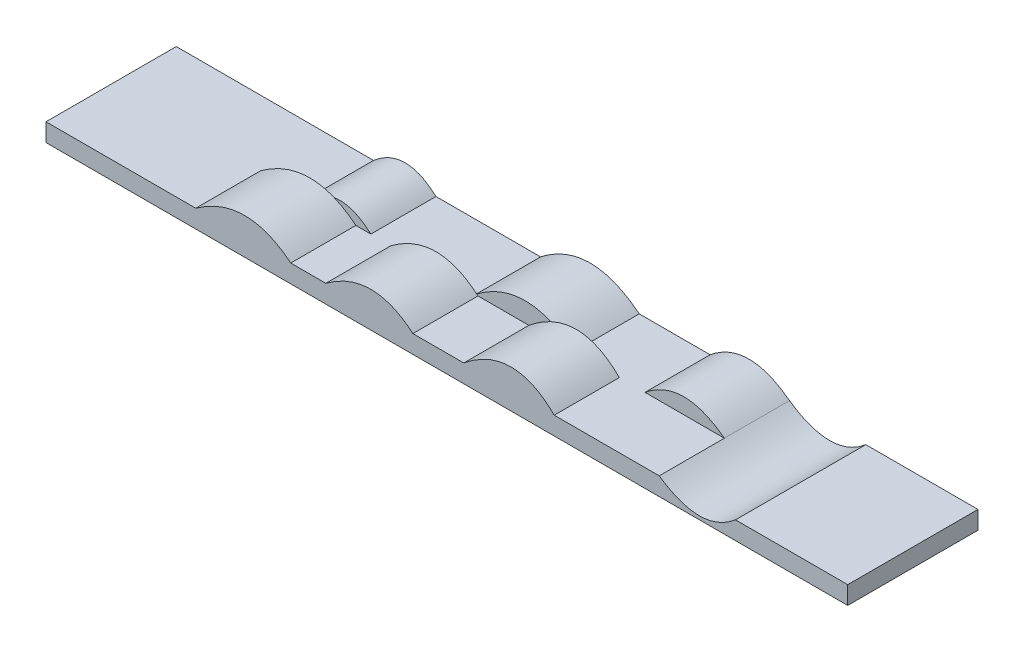
SolidWorks part; units mm, degrees
material "Pine"
ref_plane "Front Plane" through (0, 0, 0) normal (0, 0, 1) x (1, 0, 0)
ref_plane "Top Plane" through (0, 0, 0) normal (0, 1, 0) x (1, 0, 0)
ref_plane "Right Plane" through (0, 0, 0) normal (1, 0, 0) x (0, 0, -1)
sketch "Sketch1" plane through (0, 0, 0) normal (0, 1, 0) x (1, 0, 0)
  line L1 (-2000, -325) -> (2000, -325)
  line L2 (-2000, -325) -> (-2000, 325)
  line L3 (-2000, 325) -> (2000, 325)
  line L4 (2000, -325) -> (2000, 325)
  line L5 (-2000, -325) -> (2000, 325) construction
  line L6 (-2000, 325) -> (2000, -325) construction
  point P0 (0, 0)
  dimension "D1" = 650
  dimension "D2" = 4000
extrude "Boss-Extrude1" add sketch "Sketch1" along normal blind 90
sketch "Sketch2" plane through (0, 0, 325) normal (0, 0, 1) x (1, 0, 0)
  line L0 (-2000, 90) -> (2000, 90) construction
  line L1 (-1252.9038, 90) -> (535.6897, 90)
  spline S0 degree 2 poles (-1252.9038, 90) (-1001.8033, 271.3905) (-778.9548, 90) knots 0 0 0 1 1 1
  spline S1 degree 2 poles (-604.045, 90) (-371.4824, 262.9864) (-169.5917, 90) knots 0 0 0 1 1 1
  spline S2 degree 2 poles (84.3096, 90) (330.4132, 291.4597) (535.6897, 90) knots 0 0 0 1 1 1
  line M3 (2000, 90) -> (-2000, 90)
extrude "Boss-Extrude2" add sketch "Sketch2" against normal blind 325 contours S0 L1 | S1 L1 | S2 M3
sketch "Sketch3" plane through (0, 0, -325) normal (0, 0, -1) x (-1, 0, 0)
  line L0 (-2000, 90) -> (2000, 90) construction
  line L1 (-535.6897, 90) -> (-84.3096, 90) construction
  line L2 (778.9548, 90) -> (1252.9038, 90) construction
  line L3 (-1059.6872, 90) -> (1015.9293, 90)
  spline S0 degree 2 poles (-1059.6872, 90) (-853.7624, 246.421) (-663.4652, 90) knots 0 0 0 1 1 1
  spline S1 degree 2 poles (-309.9997, 90) (-66.3475, 284.5418) (182.3165, 90) knots 0 0 0 1 1 1
  spline S2 degree 2 poles (704.2628, 90) (855.8788, 227.0814) (1015.9293, 90) knots 0 0 0 1 1 1
  line M3 (2000, 90) -> (-2000, 90)
extrude "Boss-Extrude3" add sketch "Sketch3" against normal blind 325 contours S0 L3 | S1 L3 | S2 M3
sketch "Sketch4" plane through (0, 0, -325) normal (0, 0, -1) x (-1, 0, 0)
  line L0 (-2000, 90) -> (-1059.6872, 90) construction
  line L1 (-1440.181, 90) -> (-1059.6872, 90)
  spline S0 degree 2 poles (-1059.6872, 90) (-1269.4242, -55.0726) (-1440.181, 90) knots 0 0 0 1 1 1
extrude "Cut-Extrude1" cut sketch "Sketch4" against normal blind 1100
